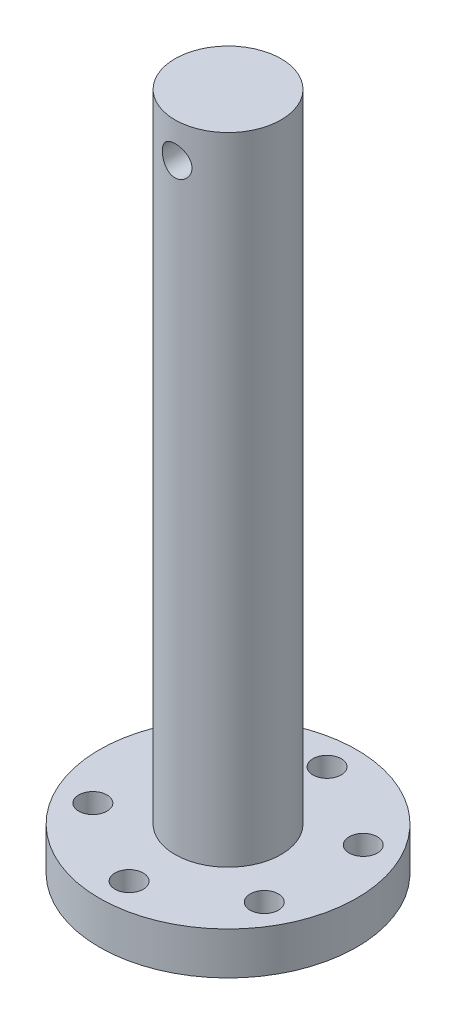
SolidWorks part; units mm, degrees
other "Markup1"
sketch "Sketch8" plane through (-18.2, 139.0587, 44.2712) normal (-0.535, 0.1154, 0.8369) x (0.8383, -0.0507, 0.5428)
other "Markup2"
sketch "Sketch10" plane through (-18.2, 96, -18.2) normal (-0.228, 0.8172, -0.5293) x (-0.8762, 0.0648, 0.4775)
ref_plane "Front Plane" through (0, 0, 0) normal (0, 0, 1) x (1, 0, 0)
ref_plane "Top Plane" through (0, 0, 0) normal (0, 1, 0) x (1, 0, 0)
ref_plane "Right Plane" through (0, 0, 0) normal (1, 0, 0) x (0, 0, -1)
sketch "Sketch1" plane through (0, 0, 0) normal (0, 1, 0) x (1, 0, 0)
  circle A0 centre (0, 0) radius 18.2
  dimension "D1" = 36.4
extrude "Boss-Extrude1" add sketch "Sketch1" along normal blind 6
sketch "Sketch3" plane through (0, 6, 0) normal (0, 1, 0) x (1, 0, 0)
  circle A0 centre (0, 14) radius 2
  dimension "D1" = 4
  dimension "D2" = 14
extrude "Cut-Extrude1" cut sketch "Sketch3" against normal blind 10
pattern_circular "CirPattern1" count 6 over 360 about axis through (0, 0, 0) along (0, 1, 0) of "Cut-Extrude1"
sketch "Sketch4" plane through (0, 6, 0) normal (0, 1, 0) x (1, 0, 0)
  circle A0 centre (0, 0) radius 7.5
  dimension "D1" = 15
extrude "Boss-Extrude2" add sketch "Sketch4" along normal blind 90
sketch "Sketch7" plane through (0, 0, 0) normal (1, 0, 0) x (0, 0, -1)
  line L0 (7.5, 96) -> (-7.5, 96) construction
  spline S0 degree 2 poles (0, 96) (-1.7427, 134.9143) (-44.0761, 130.8588) knots 0 0 0 1 1 1
ref_plane "Plane1" through (0, 0, -7.5) normal (0, 0, -1) x (-1, 0, 0)
sketch "Sketch9" plane through (0, 0, -7.5) normal (0, 0, -1) x (-1, 0, 0)
  line L0 (7.5, 96) -> (-7.5, 96) construction
  circle A0 centre (0, 91) radius 2.1
  dimension "D1" = 5
extrude "Cut-Extrude2" cut sketch "Sketch9" against normal through all
